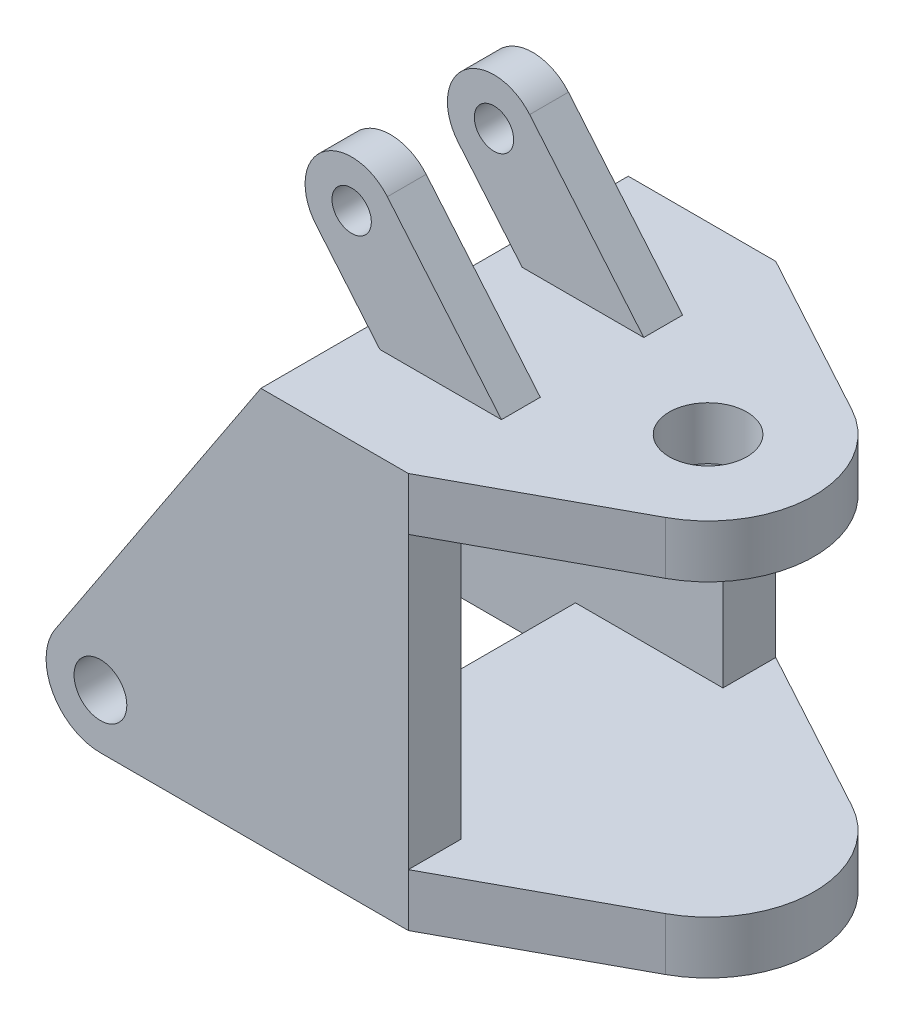
SolidWorks part; units mm, degrees
ref_plane "Front Plane" through (0, 0, 0) normal (0, 0, 1) x (1, 0, 0)
ref_plane "Top Plane" through (0, 0, 0) normal (0, 1, 0) x (1, 0, 0)
ref_plane "Right Plane" through (0, 0, 0) normal (1, 0, 0) x (0, 0, -1)
ref_plane "Plane2" through (0, 0, 355) normal (0, 0, 1) x (1, 0, 0)
sketch "Sketch2" plane through (0, 0, 355) normal (0, 0, 1) x (1, 0, 0)
  line L0 (-285, 765) -> (0, 765)
  line L1 (0, 765) -> (0, 0)
  line L2 (0, 0) -> (-595, 0)
  line L3 (-682.6201, 162.8594) -> (-285, 765)
  arc A0 (-595, 0) -> (-682.6201, 162.8594) centre (-595, 105) cw
  circle A1 centre (-595, 105) radius 51
  dimension "D4" = 102
  dimension "D5" = 105
  dimension "D1" = 765
  dimension "D2" = 285
  dimension "D3" = 595
extrude "Boss-Extrude1" add sketch "Sketch2" along normal blind 102
sketch "Sketch3" plane through (0, 765, 0) normal (0, 1, 0) x (1, 0, 0)
  line L0 (0, -457) -> (-285, -457)
  line L1 (-285, -457) -> (-285, 253)
  line L2 (-285, 253) -> (0, 253)
  line L3 (0, 253) -> (322.0192, 78.1574)
  line L4 (322.0192, -282.1574) -> (0, -457)
  line L5 (-285, -102) -> (224.2015, -102) construction
  arc A0 (322.0192, 78.1574) -> (322.0192, -282.1574) centre (224.2015, -102) cw
  circle A1 centre (224.2015, -102) radius 75
  dimension "D2" = 150
  dimension "D3" = 205
  dimension "D1" = 710
extrude "Boss-Extrude2" add sketch "Sketch3" against normal blind 102
sketch "Sketch5" plane through (0, 663, 0) normal (0, -1, 0) x (1, 0, 0)
  line L0 (429.2015, 102) -> (-285, 102)
  line L1 (-285, -253) -> (-285, 355) construction
  arc A0 (322.0192, -78.1574) -> (322.0192, 282.1574) centre (224.2015, 102) ccw construction
ref_plane "Plane8" through (0, 0, 102) normal (0, 0, 1) x (1, 0, 0)
mirror "Mirror2" about plane through (0, 0, 102) normal (0, 0, 1) of "Boss-Extrude1"
sketch "Sketch9" plane through (0, 0, 0) normal (0, -1, 0) x (1, 0, 0)
  line L7 (0, -151) -> (0, -253)
  line L8 (0, -253) -> (322.0192, -78.1574)
  line L9 (322.0192, 282.1574) -> (0, 457)
  line L10 (0, 457) -> (0, 355)
  line L11 (0, 355) -> (-285, 355)
  line L12 (-285, 355) -> (-285, -151)
  line L13 (-285, -151) -> (0, -151)
  line L14 (0, -151) -> (0, -253)
  line L15 (0, -253) -> (322.0192, -78.1574)
  line L16 (322.0192, 282.1574) -> (0, 457)
  line L17 (0, 457) -> (0, 355)
  line L18 (0, 355) -> (-285, 355)
  line L19 (-285, 355) -> (-285, -151)
  line L20 (-285, -151) -> (0, -151)
  arc A1 (322.0192, -78.1574) -> (322.0192, 282.1574) centre (224.2015, 102) ccw
  arc A2 (322.0192, -78.1574) -> (322.0192, 282.1574) centre (224.2015, 102) ccw
  dimension "D1" = 0
extrude "Boss-Extrude3" add sketch "Sketch9" against normal blind 102
sketch "Sketch17" plane through (0, 0, 102) normal (0, 0, 1) x (1, 0, 0)
  line L0 (-234.9733, 765) -> (0, 765)
  line L1 (0, 765) -> (-285, 765) construction
  line L2 (0, 663) -> (0, 765) construction
  line L3 (0, 765) -> (-220.5581, 1027.8509)
  line L4 (-234.9733, 765) -> (-358.4461, 912.1491)
  arc A0 (-358.4461, 912.1491) -> (-220.5581, 1027.8509) centre (-289.5021, 970) cw
  circle A1 centre (-289.5021, 970) radius 38
  dimension "D3" = 90
  dimension "D4" = 76
  dimension "D1" = 50
  dimension "D2" = 205
extrude "Boss-Extrude7" add sketch "Sketch17" along normal blind 75 from offset 100
mirror "Mirror5" about plane through (0, 0, 102) normal (0, 0, 1) of "Boss-Extrude7"
